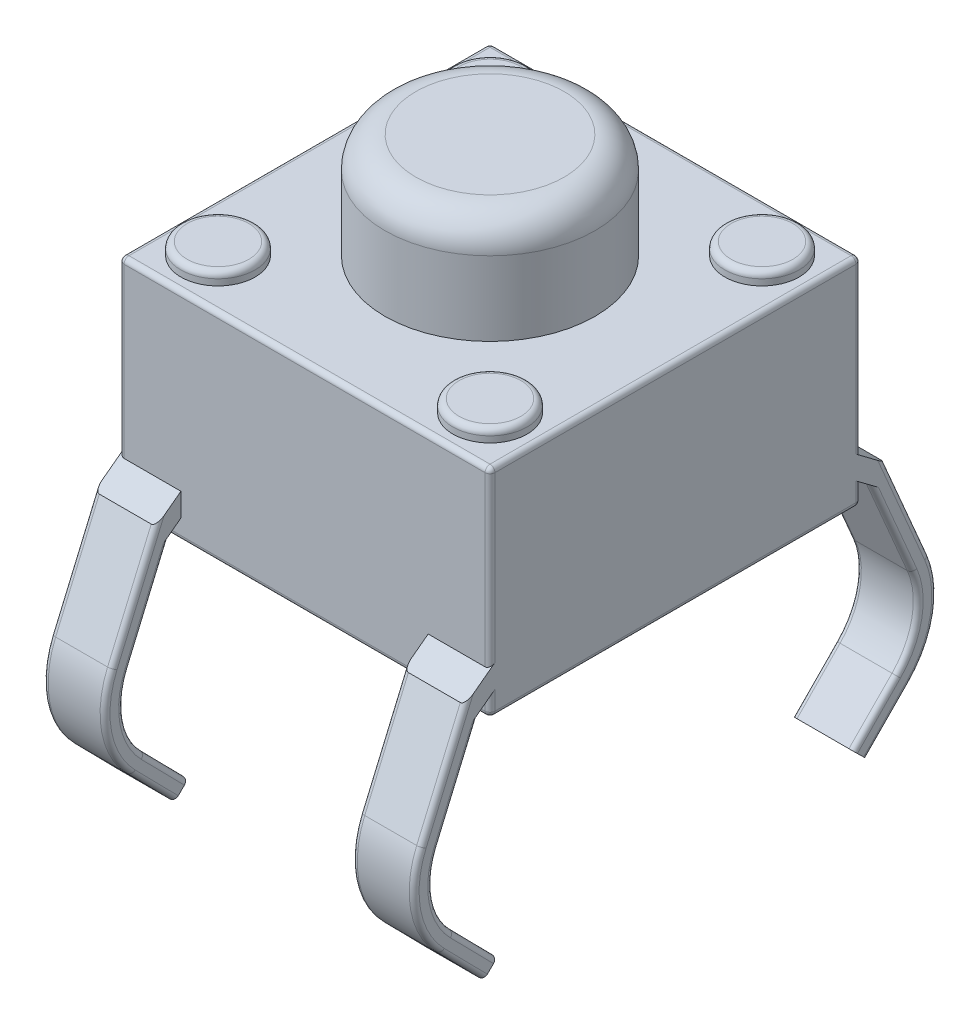
SolidWorks part; units mm, degrees
ref_plane "Front Plane" through (0, 0, 0) normal (0, 0, 1) x (1, 0, 0)
ref_plane "Top Plane" through (0, 0, 0) normal (0, 1, 0) x (1, 0, 0)
ref_plane "Right Plane" through (0, 0, 0) normal (1, 0, 0) x (0, 0, -1)
sketch "Sketch1" plane through (0, 0, 0) normal (0, 1, 0) x (1, 0, 0)
  line L1 (0, 0) -> (6, 0)
  line L2 (0, 0) -> (0, 6)
  line L3 (0, 6) -> (6, 6)
  line L4 (6, 0) -> (6, 6)
  dimension "D2" = 6
extrude "Boss-Extrude1" add sketch "Sketch1" along normal blind 3.5
sketch "Sketch2" plane through (0, 3.5, 0) normal (0, 1, 0) x (1, 0, 0)
  line L2 (0, 0) -> (6, 6) construction
  circle A0 centre (3, 3) radius 1.7
  point P4 (3, 3)
  dimension "D1" = 3.4
extrude "Boss-Extrude2" add sketch "Sketch2" along normal blind 1.7
sketch "Sketch3" plane through (0, 3.5, 0) normal (0, 1, 0) x (1, 0, 0)
  line L0 (6, 6) -> (0, 6) construction
  line L1 (0, 6) -> (0, 0) construction
  circle A0 centre (0.8, 5.2) radius 0.6
  circle A1 centre (5.2, 5.2) radius 0.6
  circle A2 centre (5.2, 0.8) radius 0.6
  circle A3 centre (0.8, 0.8) radius 0.6
  point P15 (3, 3)
  dimension "D1" = 1.2
  dimension "D2" = 0.8
  dimension "D3" = 0.8
extrude "Boss-Extrude3" add sketch "Sketch3" along normal blind 0.2
sketch "Sketch4" plane through (0, 0, 0) normal (1, 0, 0) x (0, 0, -1)
  line L0 (6, 0.7) -> (6.4002, 0.4003)
  line L1 (6, 3.5) -> (6, 0) construction
  line L2 (6.4002, 0.4003) -> (7.1063, -1.2491)
  line L3 (6.797, -2.891) -> (6.1, -3.6)
  arc A0 (7.1063, -1.2491) -> (6.797, -2.891) centre (5.7273, -1.8394) cw
  point P8 (7.5021, -2.1738)
  dimension "D4" = 1.5
  dimension "D1" = 2
  dimension "D2" = 2.8
  dimension "D3" = 0.5
  dimension "D5" = 4.3
  dimension "D6" = 0.7
  dimension "D7" = 0.1
  dimension "D8" = 150
extrude "Extrude-Thin1" add sketch "Sketch4" along normal blind 1 thin
pattern_linear "LPattern1" count 2 spacing 5 along (1, 0, 0) of "Extrude-Thin1"
ref_plane "Plane1" through (0, 0, -3) normal (0, 0, 1) x (1, 0, 0)
mirror "Mirror1" about plane through (0, 0, -3) normal (0, 0, 1) of "LPattern1", "Extrude-Thin1"
fillet "Fillet1" radius 0.1 4 edges at (0.8, 3.7, -0.2) (0.8, 3.7, -4.6) (5.2, 3.7, -4.6) (5.2, 3.7, -0.2)
fillet "Fillet2" radius 0.5 1 edges at (3, 5.2, -1.3)
fillet "Fillet13" radius 0.08 61 edges at (5, -0.5794, 0.4933) (5, -3.0352, 0.2346) (5, -0.5794, -6.4933) (5, -3.0352, -6.2346) (1, -0.5794, -6.4933) (1, -3.0352, -6.2346) (6, -0.5794, -6.4933) (6, -3.0352, -6.2346) (1, -0.5794, 0.4933) (1, -3.0352, 0.2346) (6, -0.5794, 0.4933) (6, -3.0352, 0.2346) (1, -0.4244, 0.7533) (1, -3.2455, 0.4485) (5, -0.4244, 0.7533) (5, -3.2455, 0.4485) (0, -0.5794, 0.4933) (0, -3.0352, 0.2346) (0, -0.4244, 0.7533) (0, -3.2455, 0.4485) (0, -0.4244, -6.7533) (1, -0.4244, -6.7533) (0, -3.2455, -6.4485) (1, -3.2455, -6.4485) (5, -0.4244, -6.7533) (5, -3.2455, -6.4485) (6, -0.4244, -6.7533) (6, -3.2455, -6.4485) (6, -0.4244, 0.7533) (6, -3.2455, 0.4485) (5, -2.0616, 0.9066) (5, -2.0616, -6.9066) (1, -2.0616, -6.9066) (6, -2.0616, -6.9066) (1, -2.0616, 0.9066) (6, -2.0616, 0.9066) (1, -2.1171, 1.2014) (5, -2.1171, 1.2014) (0, -2.0616, 0.9066) (0, -2.1171, 1.2014) (0, -2.1171, -7.2014) (1, -2.1171, -7.2014) (5, -2.1171, -7.2014) (6, -2.1171, -7.2014) (6, -2.1171, 1.2014) (0, 0, -3) (3, 0, 0) (6, 0, -3) (3, 0, -6) (0, 3.5, -3) (6, 3.5, -3) (3, 3.5, -6) (0, 0.1626, -6) (0, 2.1, -6) (6, 0.1626, -6) (6, 2.1, -6) (6, 0.1626, 0) (0, 0.1626, 0) (0, 2.1, 0) (6, 2.1, 0) (3, 3.5, 0)
